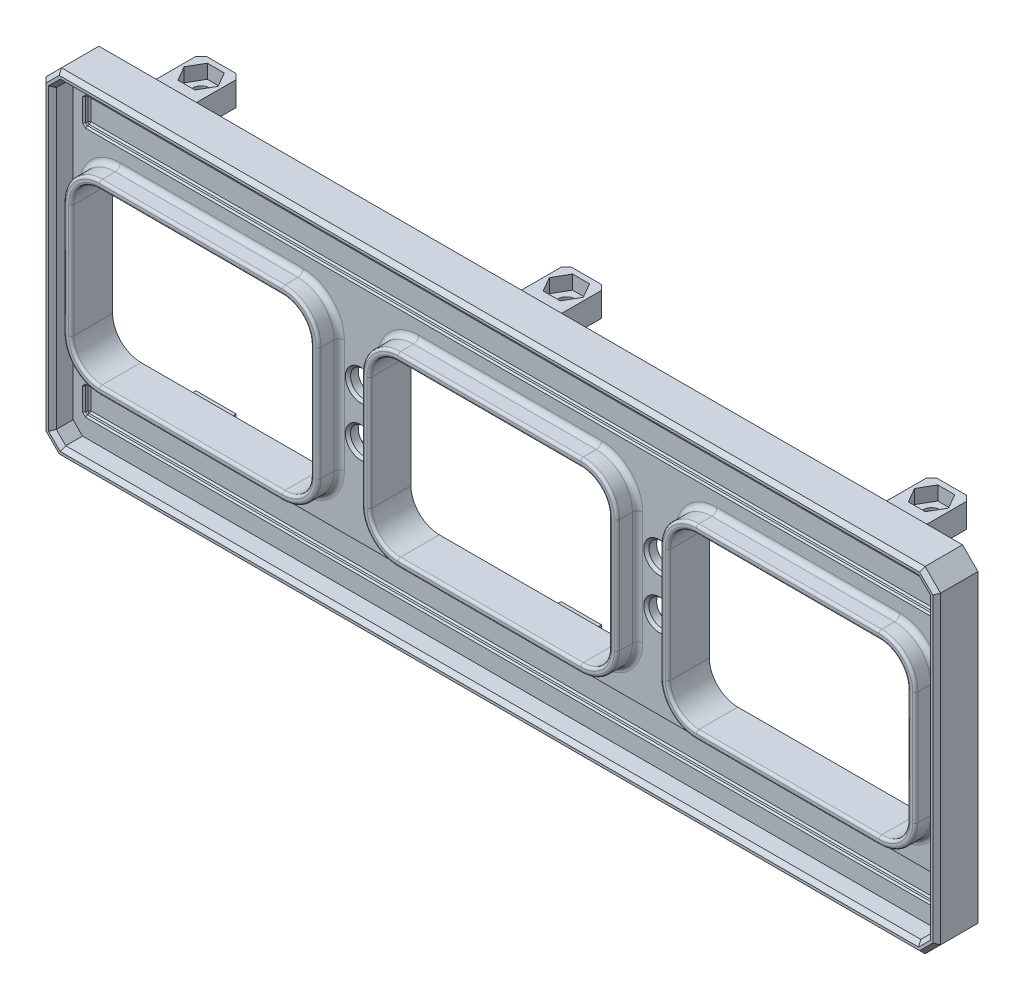
SolidWorks part; units mm, degrees
other "Markup1"
sketch "Sketch10" plane through (49.3394, 50.6504, 6) normal (0.1988, 0.1362, 0.9705) x (0.9796, 0.0028, -0.2011)
sketch "Sketch12" plane through (49.3394, 50.6504, 8) normal (0.1988, 0.1362, 0.9705) x (0.9796, 0.0028, -0.2011)
sketch "Sketch13" plane through (49.3394, 50.6504, 8) normal (0.1988, 0.1362, 0.9705) x (0.9796, 0.0028, -0.2011)
sketch "Sketch14" plane through (49.3394, 50.6504, 8) normal (0.1988, 0.1362, 0.9705) x (0.9796, 0.0028, -0.2011)
sketch "Sketch16" plane through (49.3394, 50.6504, 8) normal (0.1988, 0.1362, 0.9705) x (0.9796, 0.0028, -0.2011)
ref_plane "Front Plane" through (0, 0, 0) normal (0, 0, 1) x (1, 0, 0)
ref_plane "Top Plane" through (0, 0, 0) normal (0, 1, 0) x (1, 0, 0)
ref_plane "Right Plane" through (0, 0, 0) normal (1, 0, 0) x (0, 0, -1)
sketch "Sketch1" plane through (0, 0, 0) normal (0, 0, 1) x (1, 0, 0)
  line L0 (-60.5106, 1.6504) -> (-14.1106, 1.6504)
  line L1 (-123.9606, 50.6504) -> (49.3394, 50.6504)
  line L2 (-123.9606, 50.6504) -> (-123.9606, -14.3496)
  line L3 (-123.9606, -14.3496) -> (49.3394, -14.3496)
  line L4 (49.3394, 50.6504) -> (49.3394, -14.3496)
  line L5 (-118.3106, 34.6504) -> (-71.9106, 34.6504)
  line L6 (-118.3106, 34.6504) -> (-118.3106, 1.6504)
  line L7 (-118.3106, 1.6504) -> (-71.9106, 1.6504)
  line L8 (43.6894, 34.6504) -> (43.6894, 1.6504)
  line L10 (-71.9106, 34.6504) -> (-71.9106, 1.6504)
  line L12 (-60.5106, 34.6504) -> (-60.5106, 1.6504)
  line L14 (-14.1106, 34.6504) -> (-14.1106, 1.6504)
  line L16 (-2.7106, 34.6504) -> (-2.7106, 1.6504)
  line L17 (-60.5106, 34.6504) -> (-14.1106, 34.6504)
  line L18 (-2.7106, 1.6504) -> (43.6894, 1.6504)
  line L19 (-2.7106, 34.6504) -> (43.6894, 34.6504)
  point P10 (-118.3106, 18.1504)
  point P11 (-123.9606, 18.1504)
  dimension "D1" = 65
  dimension "D2" = 173.3
  dimension "D3" = 33
  dimension "D4" = 162
  dimension "D5" = 11.4
  dimension "D6" = 11.4
  dimension "D7" = 52.05
  dimension "D8" = 52.05
extrude "Boss-Extrude1" add sketch "Sketch1" along normal blind 4
ref_plane "Plane1" through (0, 48.5504, 0) normal (0, 1, 0) x (1, 0, 0)
ref_plane "Plane2" through (0, -12.2496, 0) normal (0, -1, 0) x (-1, 0, 0)
sketch "Sketch2" plane through (0, 48.5504, 0) normal (0, 1, 0) x (1, 0, 0)
  line L0 (-37.3106, 4.4654) -> (-37.3106, -6.4367) construction
  line L1 (49.3394, 0) -> (-123.9606, 0) construction
  line L2 (-41.2106, 0) -> (-33.4106, 0)
  line L3 (-41.2106, 0) -> (-41.2106, 10.8)
  line L4 (-41.2106, 10.8) -> (-33.4106, 10.8)
  line L5 (-33.4106, 0) -> (-33.4106, 10.8)
  line L6 (49.3394, -4) -> (-123.9606, -4) construction
  line L8 (29.5394, 0) -> (37.3394, 0)
  line L9 (29.5394, 0) -> (29.5394, 10.8)
  line L10 (29.5394, 10.8) -> (37.3394, 10.8)
  line L11 (37.3394, 0) -> (37.3394, 10.8)
  line L12 (-104.1606, 0) -> (-111.9606, 0)
  line L13 (-104.1606, 0) -> (-104.1606, 10.8)
  line L14 (-104.1606, 10.8) -> (-111.9606, 10.8)
  line L15 (-111.9606, 0) -> (-111.9606, 10.8)
  point P10 (-37.3106, -4)
  point P11 (-37.3106, 0)
  dimension "D1" = 7.8
  dimension "D2" = 10.8
  dimension "D3" = 62.95
  dimension "D4" = 62.95
extrude "Boss-Extrude2" add sketch "Sketch2" against normal blind 4.7
sketch "Sketch3" plane through (0, -12.2496, 0) normal (0, -1, 0) x (-1, 0, 0)
  line L0 (123.9606, 0) -> (-49.3394, 0) construction
  line L1 (41.2106, 10.8) -> (33.4106, 10.8)
  line L2 (41.2106, 10.8) -> (41.2106, 0)
  line L3 (41.2106, 0) -> (33.4106, 0)
  line L4 (33.4106, 10.8) -> (33.4106, 0)
  line L7 (104.1606, 0) -> (111.9606, 0)
  line L8 (104.1606, 0) -> (104.1606, 10.8)
  line L9 (104.1606, 10.8) -> (111.9606, 10.8)
  line L10 (111.9606, 0) -> (111.9606, 10.8)
  line L11 (-37.3394, 0) -> (-29.5394, 0)
  line L12 (-37.3394, 0) -> (-37.3394, 10.8)
  line L13 (-37.3394, 10.8) -> (-29.5394, 10.8)
  line L14 (-29.5394, 0) -> (-29.5394, 10.8)
extrude "Boss-Extrude3" add sketch "Sketch3" against normal blind 4.7
sketch "Sketch4" plane through (0, 48.5504, 0) normal (0, 1, 0) x (1, 0, 0)
  line L0 (-33.4106, 10.8) -> (-41.2106, 10.8) construction
  line L1 (-34.0197, 6.9) -> (-35.6652, 9.75)
  line L2 (-35.6652, 9.75) -> (-38.9561, 9.75)
  line L3 (-38.9561, 9.75) -> (-40.6015, 6.9)
  line L4 (-40.6015, 6.9) -> (-38.9561, 4.05)
  line L5 (-38.9561, 4.05) -> (-35.6652, 4.05)
  line L6 (-35.6652, 4.05) -> (-34.0197, 6.9)
  line L7 (-33.4106, 3) -> (-41.2106, 3) construction
  line L8 (-33.4106, 0) -> (-33.4106, 10.8) construction
  line L9 (-41.2106, 10.8) -> (-41.2106, 0) construction
  line L10 (49.3394, 0) -> (-123.9606, 0) construction
  line L11 (-33.4106, 3) -> (-33.4106, 10.8) construction
  line L12 (-104.1606, 10.8) -> (-111.9606, 10.8) construction
  line L13 (36.7303, 6.9) -> (35.0848, 9.75)
  line L14 (35.0848, 9.75) -> (31.7939, 9.75)
  line L15 (31.7939, 9.75) -> (30.1485, 6.9)
  line L16 (30.1485, 6.9) -> (31.7939, 4.05)
  line L17 (31.7939, 4.05) -> (35.0848, 4.05)
  line L18 (35.0848, 4.05) -> (36.7303, 6.9)
  line L19 (-104.7697, 6.9) -> (-106.4152, 9.75)
  line L20 (-106.4152, 9.75) -> (-109.7061, 9.75)
  line L21 (-109.7061, 9.75) -> (-111.3515, 6.9)
  line L22 (-111.3515, 6.9) -> (-109.7061, 4.05)
  line L23 (-109.7061, 4.05) -> (-106.4152, 4.05)
  line L24 (-106.4152, 4.05) -> (-104.7697, 6.9)
  line L25 (37.3394, 10.8) -> (29.5394, 10.8) construction
  line L26 (35.0848, 9.75) -> (35.0848, 4.05) construction
  line L27 (-35.6652, 9.75) -> (-35.6652, 4.05) construction
  line L28 (-106.4152, 9.75) -> (-106.4152, 4.05) construction
  circle A0 centre (-37.3106, 6.9) radius 2.85 construction
  circle A1 centre (33.4394, 6.9) radius 2.85 construction
  circle A2 centre (-108.0606, 6.9) radius 2.85 construction
  point P11 (-37.3106, 10.8)
  point P19 (-33.4106, 6.9)
  point P41 (-108.0606, 10.8)
  point P44 (33.4394, 10.8)
  dimension "D1" = 3
  dimension "D2" = 5.7
extrude "Cut-Extrude1" cut sketch "Sketch4" against normal blind 2.7
sketch "Sketch5" plane through (0, 45.8504, 0) normal (0, 1, 0) x (1, 0, 0)
  line L0 (-35.6652, 9.75) -> (-38.9561, 9.75) construction
  line L1 (35.0848, 9.75) -> (31.7939, 9.75) construction
  line L2 (-106.4152, 9.75) -> (-109.7061, 9.75) construction
  circle A0 centre (-37.3106, 6.9) radius 1.6
  circle A1 centre (-108.0606, 6.9) radius 1.6
  circle A2 centre (33.4394, 6.9) radius 1.6
  point P5 (-37.3106, 9.75)
  point P13 (33.4394, 9.75)
  point P19 (-108.0606, 9.75)
  dimension "D1" = 3.2
extrude "Cut-Extrude2" cut sketch "Sketch5" against normal up to surface (2 mm away) up to face at (-37.3106, 43.8504, -5.4)
sketch "Sketch6" plane through (0, -12.2496, 0) normal (0, -1, 0) x (1, 0, 0)
  line L0 (-41.2106, -3) -> (-33.4106, -3) construction
  line L1 (-34.0197, -6.9) -> (-35.6652, -4.05)
  line L2 (-35.6652, -4.05) -> (-38.9561, -4.05)
  line L3 (-38.9561, -4.05) -> (-40.6015, -6.9)
  line L4 (-40.6015, -6.9) -> (-38.9561, -9.75)
  line L5 (-38.9561, -9.75) -> (-35.6652, -9.75)
  line L6 (-35.6652, -9.75) -> (-34.0197, -6.9)
  line L7 (36.7303, -6.9) -> (35.0848, -4.05)
  line L8 (35.0848, -4.05) -> (31.7939, -4.05)
  line L9 (31.7939, -4.05) -> (30.1485, -6.9)
  line L10 (30.1485, -6.9) -> (31.7939, -9.75)
  line L11 (31.7939, -9.75) -> (35.0848, -9.75)
  line L12 (35.0848, -9.75) -> (36.7303, -6.9)
  line L13 (-104.7697, -6.9) -> (-106.4152, -4.05)
  line L14 (-106.4152, -4.05) -> (-109.7061, -4.05)
  line L15 (-109.7061, -4.05) -> (-111.3515, -6.9)
  line L16 (-111.3515, -6.9) -> (-109.7061, -9.75)
  line L17 (-109.7061, -9.75) -> (-106.4152, -9.75)
  line L18 (-106.4152, -9.75) -> (-104.7697, -6.9)
  line L19 (-41.2106, 0) -> (-41.2106, -10.8) construction
  line L20 (-33.4106, -10.8) -> (-33.4106, 0) construction
  line L21 (-33.4106, 0) -> (-41.2106, 0) construction
  line L22 (-33.4106, -3) -> (-33.4106, -10.8) construction
  line L23 (-41.2106, -10.8) -> (-33.4106, -10.8) construction
  line L24 (-35.6652, -4.05) -> (-35.6652, -9.75) construction
  line L25 (35.0848, -4.05) -> (35.0848, -9.75) construction
  line L26 (-106.4152, -4.05) -> (-106.4152, -9.75) construction
  line L27 (-111.9606, -10.8) -> (-104.1606, -10.8) construction
  line L28 (29.5394, -10.8) -> (37.3394, -10.8) construction
  circle A0 centre (-37.3106, -6.9) radius 2.85 construction
  circle A1 centre (33.4394, -6.9) radius 2.85 construction
  circle A2 centre (-108.0606, -6.9) radius 2.85 construction
  point P35 (-33.4106, -6.9)
  point P38 (-37.3106, -10.8)
  point P41 (-108.0606, -10.8)
  point P44 (33.4394, -10.8)
  dimension "D1" = 3
  dimension "D2" = 5.7
extrude "Cut-Extrude3" cut sketch "Sketch6" against normal blind 2.7
sketch "Sketch7" plane through (0, -9.5496, 0) normal (0, -1, 0) x (1, 0, 0)
  line L0 (-38.9561, -9.75) -> (-35.6652, -9.75) construction
  line L1 (-109.7061, -9.75) -> (-106.4152, -9.75) construction
  line L2 (31.7939, -9.75) -> (35.0848, -9.75) construction
  circle A0 centre (-37.3106, -6.9) radius 1.6
  circle A1 centre (33.4394, -6.9) radius 1.6
  circle A2 centre (-108.0606, -6.9) radius 1.6
  point P10 (-37.3106, -9.75)
  point P15 (-108.0606, -9.75)
  point P18 (33.4394, -9.75)
  dimension "D1" = 3.2
extrude "Cut-Extrude4" cut sketch "Sketch7" against normal up to surface (2 mm away) up to face at (-108.0606, -7.5496, -5.4)
sketch "Sketch8" plane through (0, 0, 4) normal (0, 0, 1) x (1, 0, 0)
  line L0 (49.3394, 50.6504) -> (-123.9606, 50.6504) construction
  line L1 (-123.9606, -14.3496) -> (49.3394, -14.3496) construction
  line L2 (-71.9106, 34.6504) -> (-60.5106, 34.6504) construction
  line L3 (-2.7106, 34.6504) -> (-14.1106, 34.6504) construction
  circle A0 centre (-66.2106, 23.1504) radius 2.5
  circle A1 centre (-66.2106, 13.5504) radius 2.5
  circle A2 centre (-8.4106, 23.1504) radius 2.5
  circle A3 centre (-8.4106, 13.5504) radius 2.5
  point P12 (-66.2106, 34.6504)
  point P22 (-8.4106, 34.6504)
  dimension "D3" = 5
  dimension "D1" = 27.5
  dimension "D2" = 27.9
extrude "Cut-Extrude5" cut sketch "Sketch8" against normal up to surface (4 mm away) up to face at (33.4394, -9.8996, 0)
sketch "Sketch17" plane through (0, 0, 0) normal (0, 0, -1) x (-1, 0, 0)
  line L0 (8.4106, 23.1504) -> (8.4106, 13.5504) construction
  line L1 (37.3106, 1.6504) -> (37.3106, 34.6504) construction
  line L2 (4.9106, 9.8504) -> (11.9106, 9.8504)
  line L3 (3.9106, 10.8504) -> (3.9106, 25.8504)
  line L4 (4.9106, 26.8504) -> (11.9106, 26.8504)
  line L5 (12.9106, 10.8504) -> (12.9106, 25.8504)
  line L6 (3.9106, 9.8504) -> (12.9106, 26.8504) construction
  line L7 (3.9106, 26.8504) -> (12.9106, 9.8504) construction
  line L8 (60.5106, 1.6504) -> (14.1106, 1.6504) construction
  line L13 (14.1106, 34.6504) -> (60.5106, 34.6504) construction
  line L14 (69.7106, 26.8504) -> (62.7106, 26.8504)
  line L15 (61.7106, 10.8504) -> (61.7106, 25.8504)
  line L16 (69.7106, 9.8504) -> (62.7106, 9.8504)
  line L17 (70.7106, 10.8504) -> (70.7106, 25.8504)
  arc A0 (4.9106, 9.8504) -> (3.9106, 10.8504) centre (4.9106, 10.8504) cw
  arc A1 (11.9106, 9.8504) -> (12.9106, 10.8504) centre (11.9106, 10.8504) ccw
  arc A2 (3.9106, 25.8504) -> (4.9106, 26.8504) centre (4.9106, 25.8504) cw
  arc A3 (12.9106, 25.8504) -> (11.9106, 26.8504) centre (11.9106, 25.8504) ccw
  arc A4 (61.7106, 25.8504) -> (62.7106, 26.8504) centre (62.7106, 25.8504) cw
  arc A5 (62.7106, 9.8504) -> (61.7106, 10.8504) centre (62.7106, 10.8504) cw
  arc A6 (69.7106, 9.8504) -> (70.7106, 10.8504) centre (69.7106, 10.8504) ccw
  arc A7 (70.7106, 25.8504) -> (69.7106, 26.8504) centre (69.7106, 25.8504) ccw
  point P4 (8.4106, 18.3504)
  point P9 (66.2106, 18.3504)
  point P12 (8.4106, 18.3504)
  dimension "D3" = 1
  dimension "D1" = 17
  dimension "D2" = 9
extrude "Cut-Extrude8" cut sketch "Sketch17" against normal blind 2
chamfer "Chamfer1" distance 1 angle 45 18 edges at (-111.9606, -9.8996, -10.8) (-108.0606, -7.5496, -10.8) (-104.1606, -9.8996, -10.8) (-111.9606, 46.2004, -10.8) (-108.0606, 43.8504, -10.8) (-104.1606, 46.2004, -10.8) (-41.2106, -9.8996, -10.8) (-37.3106, -7.5496, -10.8) (-33.4106, -9.8996, -10.8) (-41.2106, 46.2004, -10.8) (-37.3106, 43.8504, -10.8) (-33.4106, 46.2004, -10.8) (29.5394, -9.8996, -10.8) (33.4394, -7.5496, -10.8) (37.3394, -9.8996, -10.8) (29.5394, 46.2004, -10.8) (33.4394, 43.8504, -10.8) (37.3394, 46.2004, -10.8)
sketch "Sketch9" plane through (0, 0, 4) normal (0, 0, 1) x (1, 0, 0)
  line L0 (-71.9106, 34.6504) -> (-118.3106, 34.6504) construction
  line L1 (-119.8106, 36.1504) -> (-70.4106, 36.1504)
  line L2 (-119.8106, 36.1504) -> (-119.8106, 0.1504)
  line L3 (-119.8106, 0.1504) -> (-70.4106, 0.1504)
  line L4 (-70.4106, 36.1504) -> (-70.4106, 0.1504)
  line L7 (-118.3106, 34.6504) -> (-118.3106, 1.6504) construction
  line L8 (-62.0106, 36.1504) -> (-62.0106, 0.1504)
  line L9 (-71.9106, 34.6504) -> (-118.3106, 34.6504)
  line L10 (-71.9106, 34.6504) -> (-71.9106, 1.6504)
  line L11 (-71.9106, 1.6504) -> (-118.3106, 1.6504)
  line L12 (-118.3106, 34.6504) -> (-118.3106, 1.6504)
  line L13 (-62.0106, 36.1504) -> (-12.6106, 36.1504)
  line L14 (-12.6106, 36.1504) -> (-12.6106, 0.1504)
  line L15 (-62.0106, 0.1504) -> (-12.6106, 0.1504)
  line L16 (-14.1106, 34.6504) -> (-14.1106, 1.6504)
  line L17 (-14.1106, 34.6504) -> (-60.5106, 34.6504)
  line L18 (-60.5106, 34.6504) -> (-60.5106, 1.6504)
  line L19 (-14.1106, 1.6504) -> (-60.5106, 1.6504)
  line L20 (-4.2106, 36.1504) -> (-4.2106, 0.1504)
  line L21 (-4.2106, 36.1504) -> (45.1894, 36.1504)
  line L22 (45.1894, 36.1504) -> (45.1894, 0.1504)
  line L23 (-4.2106, 0.1504) -> (45.1894, 0.1504)
  line L24 (43.6894, 34.6504) -> (43.6894, 1.6504)
  line L25 (43.6894, 34.6504) -> (-2.7106, 34.6504)
  line L26 (-2.7106, 34.6504) -> (-2.7106, 1.6504)
  line L27 (43.6894, 1.6504) -> (-2.7106, 1.6504)
  line L29 (49.3394, 50.6504) -> (-123.9606, 50.6504)
  line L30 (49.3394, 50.6504) -> (49.3394, -14.3496)
  line L31 (49.3394, -14.3496) -> (-123.9606, -14.3496)
  line L32 (-123.9606, 50.6504) -> (-123.9606, -14.3496)
  line L33 (47.3394, 48.6504) -> (-121.9606, 48.6504)
  line L34 (47.3394, 48.6504) -> (47.3394, -12.3496)
  line L35 (47.3394, -12.3496) -> (-121.9606, -12.3496)
  line L36 (-121.9606, 48.6504) -> (-121.9606, -12.3496)
  point P6 (-95.1106, 34.6504)
  point P7 (-95.1106, 36.1504)
  point P8 (-70.4106, 18.1504)
  point P9 (-71.9106, 18.1504)
  point P44 (47.3394, 18.1504)
  point P45 (49.3394, 18.1504)
  point P46 (-37.3106, 48.6504)
  point P47 (-37.3106, 50.6504)
  line M21 (-123.9606, 50.6504) -> (-123.9606, -14.3496)
  line M22 (-123.9606, -14.3496) -> (49.3394, -14.3496)
  line M23 (49.3394, -14.3496) -> (49.3394, 50.6504)
  line M24 (49.3394, 50.6504) -> (-123.9606, 50.6504)
  line M25 (-71.9106, 1.6504) -> (-118.3106, 1.6504)
  line M26 (-118.3106, 1.6504) -> (-118.3106, 34.6504)
  line M27 (-118.3106, 34.6504) -> (-71.9106, 34.6504)
  line M28 (-71.9106, 34.6504) -> (-71.9106, 1.6504)
  line M29 (43.6894, 34.6504) -> (43.6894, 1.6504)
  line M30 (43.6894, 1.6504) -> (-2.7106, 1.6504)
  line M31 (-2.7106, 1.6504) -> (-2.7106, 34.6504)
  line M32 (-2.7106, 34.6504) -> (43.6894, 34.6504)
  line M33 (-14.1106, 1.6504) -> (-60.5106, 1.6504)
  line M34 (-60.5106, 1.6504) -> (-60.5106, 34.6504)
  line M35 (-60.5106, 34.6504) -> (-14.1106, 34.6504)
  line M36 (-14.1106, 34.6504) -> (-14.1106, 1.6504)
  dimension "D1" = 1.5
  dimension "D4" = 1.5
  dimension "D6" = 8.4
  dimension "D7" = 2
  dimension "D8" = 2
  dimension "D5" = 3
extrude "Boss-Extrude4" add sketch "Sketch9" along normal blind 4 contours L4 L1 L2 L3 M28 M25 M26 M27 | L8 L15 L14 L13 M36 M33 M34 M35 | L20 L23 L22 L21 M32 M29 M30 M31 | L36 L33 L34 L35 M24 M21 M22 M23
sketch "Sketch11" plane through (0, 0, 4) normal (0, 0, 1) x (1, 0, 0)
  line L0 (45.1894, 36.1504) -> (45.1894, 0.1504) construction
  line L1 (-119.8106, 39.9004) -> (45.1894, 39.9004)
  line L2 (-119.8106, 39.9004) -> (-119.8106, 44.9004)
  line L3 (-119.8106, 44.9004) -> (45.1894, 44.9004)
  line L4 (45.1894, 39.9004) -> (45.1894, 44.9004)
  line L5 (-119.8106, 36.1504) -> (-119.8106, 0.1504) construction
  line L6 (-4.2106, 36.1504) -> (45.1894, 36.1504) construction
  line L7 (45.1894, 36.1504) -> (45.1894, 39.9004) construction
  line L8 (45.1894, -3.5996) -> (-119.8106, -3.5996)
  line L9 (45.1894, -3.5996) -> (45.1894, -8.5996)
  line L10 (45.1894, -8.5996) -> (-119.8106, -8.5996)
  line L11 (-119.8106, -3.5996) -> (-119.8106, -8.5996)
  line L12 (45.1894, -3.5996) -> (45.1894, 0.1504) construction
  dimension "D1" = 5
  dimension "D2" = 3.75
extrude "Cut-Extrude6" cut sketch "Sketch11" against normal blind 1
sketch "Sketch15" plane through (0, 0, 0) normal (0, 0, -1) x (-1, 0, 0)
  circle A0 centre (8.4106, 30.1504) radius 2.85
  circle A1 centre (8.4106, 6.1504) radius 2.85
  circle A2 centre (66.2106, 30.1504) radius 2.85
  circle A3 centre (66.2106, 6.1504) radius 2.85
  dimension "D1" = 5.7
  dimension "D2" = 7
  dimension "D3" = 7.4
extrude "Cut-Extrude7" cut sketch "Sketch15" against normal blind 2.5
chamfer "Chamfer3" distance 3 angle 45 4 edges at (49.3394, -14.3496, 4) (49.3394, 50.6504, 4) (-123.9606, 50.6504, 4) (-123.9606, -14.3496, 4)
chamfer "Chamfer5" distance 1.8284 angle 45 4 edges at (-121.9606, -12.3496, 6) (47.3394, -12.3496, 6) (47.3394, 48.6504, 6) (-121.9606, 48.6504, 6)
chamfer "Chamfer6" distance 0.75 angle 45 16 edges at (46.4252, -11.4354, 8) (47.3394, 18.1504, 8) (46.4252, 47.7362, 8) (-37.3106, 48.6504, 8) (-121.0464, 47.7362, 8) (-37.3106, -12.3496, 8) (-121.0464, -11.4354, 8) (-121.9606, 18.1504, 8) (-122.4606, 49.1504, 8) (-37.3106, 50.6504, 8) (47.8394, 49.1504, 8) (49.3394, 18.1504, 8) (47.8394, -12.8496, 8) (-37.3106, -14.3496, 8) (-122.4606, -12.8496, 8) (-123.9606, 18.1504, 8)
chamfer "Chamfer8" distance 0.3 angle 45 24 edges at (-37.3106, 44.9004, 3) (-119.8106, 42.4004, 3) (-119.8106, 44.9004, 3.5) (-37.3106, 44.9004, 4) (-119.8106, 42.4004, 4) (45.1894, 42.4004, 3) (-37.3106, 39.9004, 3) (45.1894, 39.9004, 3.5) (45.1894, 42.4004, 4) (45.1894, 44.9004, 3.5) (-119.8106, 39.9004, 3.5) (-37.3106, 39.9004, 4) (45.1894, -6.0996, 4) (-119.8106, -6.0996, 4) (-119.8106, -8.5996, 3.5) (-37.3106, -8.5996, 4) (45.1894, -8.5996, 3.5) (45.1894, -3.5996, 3.5) (-37.3106, -3.5996, 4) (-119.8106, -3.5996, 3.5) (-37.3106, -8.5996, 3) (-119.8106, -6.0996, 3) (-37.3106, -3.5996, 3) (45.1894, -6.0996, 3)
chamfer "Chamfer9" distance 0.5 angle 45 4 edges at (-5.9106, 13.5504, 4) (-5.9106, 23.1504, 4) (-63.7106, 13.5504, 4) (-63.7106, 23.1504, 4)
fillet "Fillet3" radius 5.5 12 edges at (-118.3106, 1.6504, 4) (-71.9106, 1.6504, 4) (-71.9106, 34.6504, 4) (-118.3106, 34.6504, 4) (-14.1106, 1.6504, 4) (43.6894, 1.6504, 4) (-2.7106, 1.6504, 4) (-60.5106, 1.6504, 4) (-60.5106, 34.6504, 4) (-2.7106, 34.6504, 4) (43.6894, 34.6504, 4) (-14.1106, 34.6504, 4)
fillet "Fillet4" radius 7 12 edges at (-119.8106, 0.1504, 6) (-119.8106, 36.1504, 6) (-70.4106, 36.1504, 6) (-70.4106, 0.1504, 6) (45.1894, 0.1504, 6) (45.1894, 36.1504, 6) (-12.6106, 36.1504, 6) (-62.0106, 36.1504, 6) (-4.2106, 36.1504, 6) (-4.2106, 0.1504, 6) (-12.6106, 0.1504, 6) (-62.0106, 0.1504, 6)
fillet "Fillet5" radius 1 24 edges at (-117.7604, 2.2006, 4) (-119.8106, 18.1504, 4) (-117.7604, 34.1001, 4) (-95.1106, 36.1504, 4) (-72.4609, 34.1001, 4) (-70.4106, 18.1504, 4) (-72.4609, 2.2006, 4) (-95.1106, 0.1504, 4) (-2.1604, 2.2006, 4) (-4.2106, 18.1504, 4) (-2.1604, 34.1001, 4) (20.4894, 36.1504, 4) (43.1391, 34.1001, 4) (45.1894, 18.1504, 4) (43.1391, 2.2006, 4) (-59.9604, 2.2006, 4) (-62.0106, 18.1504, 4) (-59.9604, 34.1001, 4) (-37.3106, 36.1504, 4) (-14.6609, 34.1001, 4) (-12.6106, 18.1504, 4) (-14.6609, 2.2006, 4) (20.4894, 0.1504, 4) (-37.3106, 0.1504, 4)
fillet "Fillet6" radius 0.5 48 edges at (-73.5215, 33.0395, 8) (-95.1106, 34.6504, 8) (-116.6997, 33.0395, 8) (-118.3106, 18.1504, 8) (-116.6997, 3.2613, 8) (-95.1106, 1.6504, 8) (-73.5215, 3.2613, 8) (-72.4609, 34.1001, 8) (-95.1106, 36.1504, 8) (-117.7604, 34.1001, 8) (-119.8106, 18.1504, 8) (-117.7604, 2.2006, 8) (-95.1106, 0.1504, 8) (-72.4609, 2.2006, 8) (-71.9106, 18.1504, 8) (-70.4106, 18.1504, 8) (20.4894, 1.6504, 8) (42.0785, 3.2613, 8) (43.6894, 18.1504, 8) (42.0785, 33.0395, 8) (20.4894, 34.6504, 8) (-1.0997, 33.0395, 8) (-2.7106, 18.1504, 8) (-4.2106, 18.1504, 8) (-2.1604, 34.1001, 8) (20.4894, 36.1504, 8) (43.1391, 34.1001, 8) (45.1894, 18.1504, 8) (43.1391, 2.2006, 8) (20.4894, 0.1504, 8) (-37.3106, 0.1504, 8) (-59.9604, 2.2006, 8) (-62.0106, 18.1504, 8) (-59.9604, 34.1001, 8) (-37.3106, 36.1504, 8) (-14.6609, 34.1001, 8) (-12.6106, 18.1504, 8) (-14.1106, 18.1504, 8) (-15.7215, 33.0395, 8) (-37.3106, 34.6504, 8) (-58.8997, 33.0395, 8) (-60.5106, 18.1504, 8) (-58.8997, 3.2613, 8) (-37.3106, 1.6504, 8) (-1.0997, 3.2613, 8) (-2.1604, 2.2006, 8) (-14.6609, 2.2006, 8) (-15.7215, 3.2613, 8)
equation "\"w\"=1.41421"
